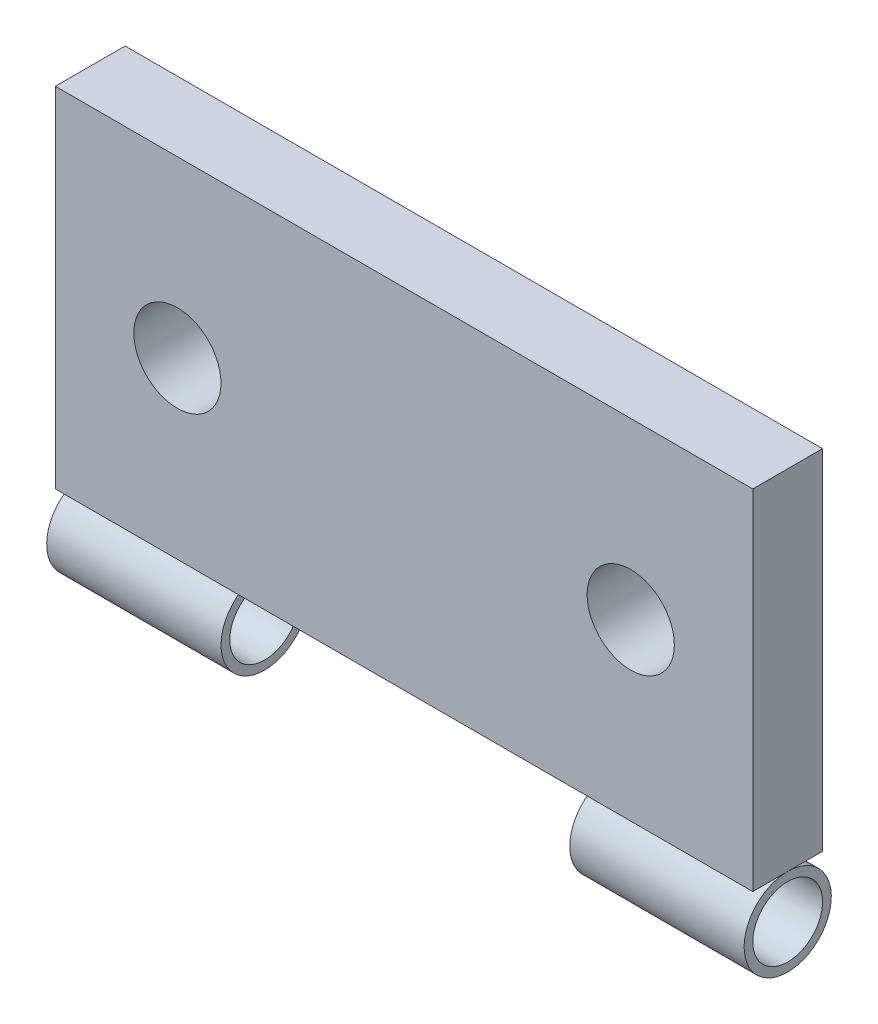
SolidWorks part; units mm, degrees
ref_plane "Front Plane" through (0, 0, 0) normal (0, 0, 1) x (1, 0, 0)
ref_plane "Top Plane" through (0, 0, 0) normal (0, 1, 0) x (1, 0, 0)
ref_plane "Right Plane" through (0, 0, 0) normal (1, 0, 0) x (0, 0, -1)
sketch "Sketch1" plane through (0, 0, 0) normal (0, 0, 1) x (1, 0, 0)
  line L1 (-20, 10) -> (20, 10)
  line L2 (-20, 10) -> (-20, -10)
  line L3 (-20, -10) -> (20, -10)
  line L4 (20, 10) -> (20, -10)
  line L5 (-20, 10) -> (20, -10) construction
  line L6 (-20, -10) -> (20, 10) construction
  circle A0 centre (-13, 0) radius 2.5
  circle A1 centre (13, 0) radius 2.5
  point P0 (0, 0)
  dimension "D3" = 5
  dimension "D1" = 40
  dimension "D2" = 20
  dimension "D4" = 7
  dimension "D5" = 7
extrude "Boss-Extrude1" add sketch "Sketch1" along normal mid plane 4
sketch "Sketch3" plane through (-20, 0, 0) normal (-1, 0, 0) x (0, 0, 1)
  line L1 (2, -10) -> (-2, -10) construction
  circle A0 centre (-0.0033, -12.5) radius 2.5
  circle A1 centre (-0.0033, -12.5) radius 2
  point P3 (0, 0)
  dimension "D1" = 5
  dimension "D2" = 4
extrude "Boss-Extrude2" add sketch "Sketch3" against normal blind 40 separate body
sketch "Sketch4" plane through (0, 0, 2) normal (0, 0, 1) x (1, 0, 0)
  line L0 (-20, -10) -> (20, -10) construction
  line L1 (-10, -10) -> (10, -10)
  line L2 (-10, -10) -> (-10, -15.1807)
  line L3 (-10, -15.1807) -> (10, -15.1807)
  line L4 (10, -10) -> (10, -15.1807)
  point P6 (0, -10)
  dimension "D1" = 20
extrude "Cut-Extrude1" cut sketch "Sketch4" against normal mid plane 10
